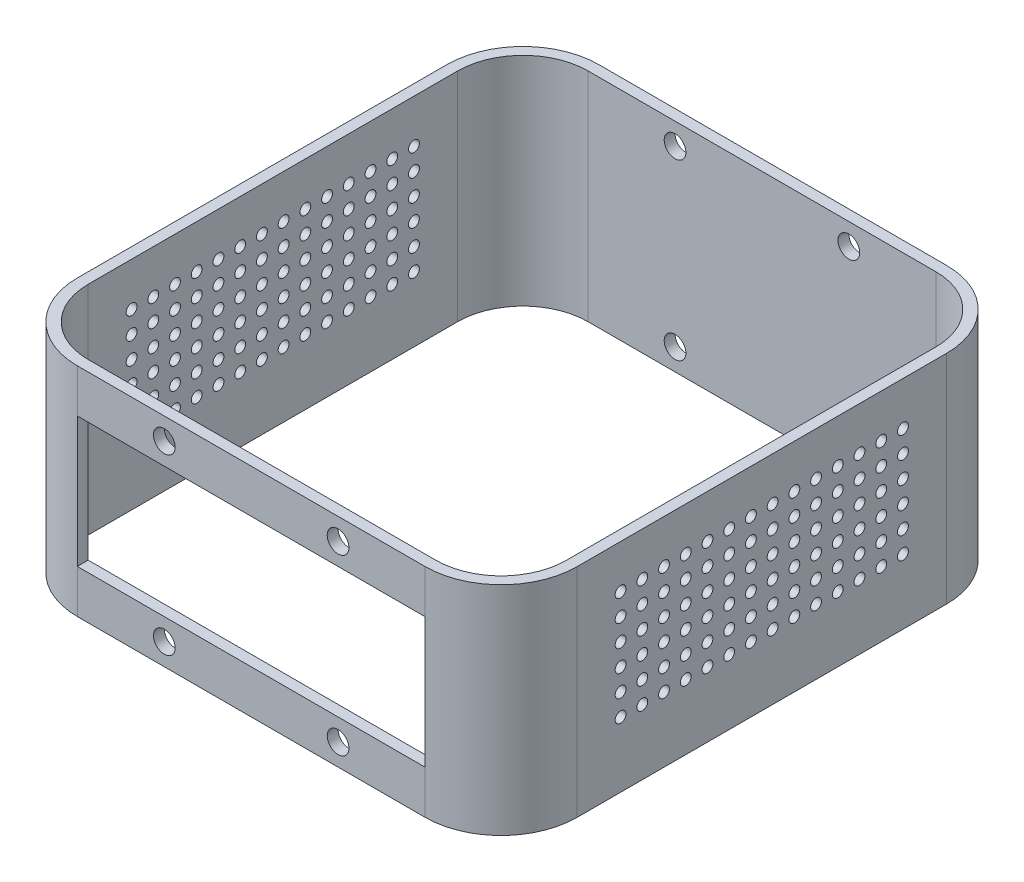
SolidWorks part; units mm, degrees
ref_plane "Front Plane" through (0, 0, 0) normal (0, 0, 1) x (1, 0, 0)
ref_plane "Top Plane" through (0, 0, 0) normal (0, 1, 0) x (1, 0, 0)
ref_plane "Right Plane" through (0, 0, 0) normal (1, 0, 0) x (0, 0, -1)
sketch "Sketch1" plane through (0, 0, 0) normal (0, 1, 0) x (1, 0, 0)
  line L0 (356.5379, 539.6819) -> (1600.9879, 539.6819) construction
  line L1 (-5, 30) -> (-5, 200.15)
  line L2 (30, 0) -> (190.15, 0)
  line L3 (0, 30) -> (0, 200.15)
  line L4 (30, 230.15) -> (190.15, 230.15)
  line L5 (220.15, 30) -> (220.15, 200.15)
  line L6 (30, 235.15) -> (190.15, 235.15)
  line L7 (225.15, 30) -> (225.15, 200.15)
  line L8 (30, -5) -> (190.15, -5)
  arc A0 (30, 230.15) -> (0, 200.15) centre (30, 200.15) ccw
  arc A1 (190.15, 230.15) -> (220.15, 200.15) centre (190.15, 200.15) cw
  arc A2 (220.15, 30) -> (190.15, 0) centre (190.15, 30) cw
  arc A3 (0, 30) -> (30, 0) centre (30, 30) ccw
  arc A4 (30, 235.15) -> (-5, 200.15) centre (30, 200.15) ccw
  arc A5 (190.15, 235.15) -> (225.15, 200.15) centre (190.15, 200.15) cw
  arc A6 (225.15, 30) -> (190.15, -5) centre (190.15, 30) cw
  arc A7 (-5, 30) -> (30, -5) centre (30, 30) ccw
  point P13 (220.15, 0)
  point P16 (0, 0)
  dimension "D3" = 30
  dimension "D1" = 230.15
  dimension "D2" = 220.15
  dimension "D4" = 5
extrude "Boss-Extrude1" add sketch "Sketch1" along normal blind 100
sketch "Sketch3" plane through (-5, 0, 0) normal (-1, 0, 0) x (0, 0, 1)
  line L1 (-200.15, 0) -> (-185.15, 0)
  line L2 (-200.15, 0) -> (-200.15, 20)
  line L3 (-200.15, 20) -> (-185.15, 20)
  line L4 (-185.15, 0) -> (-185.15, 20)
  line L5 (-185.15, 0) -> (-185.15, 20)
  line L6 (-185.15, 0) -> (-170.15, 0)
  line L7 (-170.15, 0) -> (-170.15, 20)
  line L8 (-185.15, 20) -> (-170.15, 20)
  line L9 (-170.15, 0) -> (-170.15, 20)
  line L10 (-170.15, 0) -> (-155.15, 0)
  line L11 (-155.15, 0) -> (-155.15, 20)
  line L12 (-170.15, 20) -> (-155.15, 20)
  line L13 (-155.15, 0) -> (-155.15, 20)
  line L14 (-155.15, 0) -> (-140.15, 0)
  line L15 (-140.15, 0) -> (-140.15, 20)
  line L16 (-155.15, 20) -> (-140.15, 20)
  line L17 (-140.15, 0) -> (-140.15, 20)
  line L18 (-140.15, 0) -> (-125.15, 0)
  line L19 (-125.15, 0) -> (-125.15, 20)
  line L20 (-140.15, 20) -> (-125.15, 20)
  line L21 (-125.15, 0) -> (-125.15, 20)
  line L22 (-125.15, 0) -> (-110.15, 0)
  line L23 (-110.15, 0) -> (-110.15, 20)
  line L24 (-125.15, 20) -> (-110.15, 20)
  line L25 (-110.15, 0) -> (-110.15, 20)
  line L26 (-110.15, 0) -> (-95.15, 0)
  line L27 (-95.15, 0) -> (-95.15, 20)
  line L28 (-110.15, 20) -> (-95.15, 20)
  line L29 (-95.15, 0) -> (-95.15, 20)
  line L30 (-95.15, 0) -> (-80.15, 0)
  line L31 (-80.15, 0) -> (-80.15, 20)
  line L32 (-95.15, 20) -> (-80.15, 20)
  line L33 (-80.15, 0) -> (-80.15, 20)
  line L34 (-80.15, 0) -> (-65.15, 0)
  line L35 (-65.15, 0) -> (-65.15, 20)
  line L36 (-80.15, 20) -> (-65.15, 20)
  line L37 (-65.15, 0) -> (-65.15, 20)
  line L38 (-65.15, 0) -> (-50.15, 0)
  line L39 (-50.15, 0) -> (-50.15, 20)
  line L40 (-65.15, 20) -> (-50.15, 20)
  line L41 (-50.15, 0) -> (-50.15, 20)
  line L42 (-50.15, 0) -> (-35.15, 0)
  line L43 (-35.15, 0) -> (-35.15, 20)
  line L44 (-50.15, 20) -> (-35.15, 20)
  line L45 (-35.15, 0) -> (-35.15, 20)
  line L46 (-35.15, 0) -> (-20.15, 0)
  line L47 (-20.15, 0) -> (-20.15, 20)
  line L48 (-35.15, 20) -> (-20.15, 20)
  line L49 (-20.15, 0) -> (-20.15, 20)
  line L50 (-20.15, 0) -> (-5.15, 0)
  line L51 (-5.15, 0) -> (-5.15, 20)
  line L52 (-20.15, 20) -> (-5.15, 20)
  line L53 (-5.15, 0) -> (-5.15, 20)
  line L54 (-5.15, 0) -> (9.85, 0)
  line L55 (9.85, 0) -> (9.85, 20)
  line L56 (-5.15, 20) -> (9.85, 20)
  line L57 (9.85, 0) -> (9.85, 20)
  line L58 (9.85, 0) -> (24.85, 0)
  line L59 (24.85, 0) -> (24.85, 20)
  line L60 (9.85, 20) -> (24.85, 20)
  line L61 (24.85, 0) -> (24.85, 20)
  line L62 (24.85, 0) -> (39.85, 0)
  line L63 (39.85, 0) -> (39.85, 20)
  line L64 (24.85, 20) -> (39.85, 20)
  line M3 (-200.15, 0) -> (-30, 0)
  line M5 (-30, 100) -> (-200.15, 100)
  line M6 (-200.15, 100) -> (-200.15, 0)
  dimension "D1" = 15
  dimension "D3" = 20
  dimension "D2" = 16
extrude "Boss-Extrude2" [suppressed] add sketch "Sketch3" against normal blind 20 contours L4 M3 M5 M6 | L11 L7 M3 M5 | L19 L15 M3 M5 | L35 L31 M3 M5 | L43 L39 M3 M5 | L51 L47 M3 M5 | L27 L28 L25 L26
sketch "Sketch4" plane through (225.15, 0, 0) normal (1, 0, 0) x (0, 0, -1)
  line L1 (200.15, 0) -> (185.15, 0)
  line L2 (200.15, 0) -> (200.15, 20)
  line L3 (200.15, 20) -> (185.15, 20)
  line L4 (185.15, 0) -> (185.15, 20)
  line L5 (185.15, 0) -> (185.15, 20)
  line L6 (185.15, 0) -> (170.15, 0)
  line L7 (170.15, 0) -> (170.15, 20)
  line L8 (185.15, 20) -> (170.15, 20)
  line L9 (170.15, 0) -> (170.15, 20)
  line L10 (170.15, 0) -> (155.15, 0)
  line L11 (155.15, 0) -> (155.15, 20)
  line L12 (170.15, 20) -> (155.15, 20)
  line L13 (155.15, 0) -> (155.15, 20)
  line L14 (155.15, 0) -> (140.15, 0)
  line L15 (140.15, 0) -> (140.15, 20)
  line L16 (155.15, 20) -> (140.15, 20)
  line L17 (140.15, 0) -> (140.15, 20)
  line L18 (140.15, 0) -> (125.15, 0)
  line L19 (125.15, 0) -> (125.15, 20)
  line L20 (140.15, 20) -> (125.15, 20)
  line L21 (125.15, 0) -> (125.15, 20)
  line L22 (125.15, 0) -> (110.15, 0)
  line L23 (110.15, 0) -> (110.15, 20)
  line L24 (125.15, 20) -> (110.15, 20)
  line L25 (110.15, 0) -> (110.15, 20)
  line L26 (110.15, 0) -> (95.15, 0)
  line L27 (95.15, 0) -> (95.15, 20)
  line L28 (110.15, 20) -> (95.15, 20)
  line L29 (95.15, 0) -> (95.15, 20)
  line L30 (95.15, 0) -> (80.15, 0)
  line L31 (80.15, 0) -> (80.15, 20)
  line L32 (95.15, 20) -> (80.15, 20)
  line L33 (80.15, 0) -> (80.15, 20)
  line L34 (80.15, 0) -> (65.15, 0)
  line L35 (65.15, 0) -> (65.15, 20)
  line L36 (80.15, 20) -> (65.15, 20)
  line L37 (65.15, 0) -> (65.15, 20)
  line L38 (65.15, 0) -> (50.15, 0)
  line L39 (50.15, 0) -> (50.15, 20)
  line L40 (65.15, 20) -> (50.15, 20)
  line L41 (50.15, 0) -> (50.15, 20)
  line L42 (50.15, 0) -> (35.15, 0)
  line L43 (35.15, 0) -> (35.15, 20)
  line L44 (50.15, 20) -> (35.15, 20)
  line L45 (35.15, 0) -> (35.15, 20)
  line L46 (35.15, 0) -> (20.15, 0)
  line L47 (20.15, 0) -> (20.15, 20)
  line L48 (35.15, 20) -> (20.15, 20)
  line L49 (20.15, 0) -> (20.15, 20)
  line L50 (20.15, 0) -> (5.15, 0)
  line L51 (5.15, 0) -> (5.15, 20)
  line L52 (20.15, 20) -> (5.15, 20)
  line L53 (5.15, 0) -> (5.15, 20)
  line L54 (5.15, 0) -> (-9.85, 0)
  line L55 (-9.85, 0) -> (-9.85, 20)
  line L56 (5.15, 20) -> (-9.85, 20)
  line L57 (-9.85, 0) -> (-9.85, 20)
  line L58 (-9.85, 0) -> (-24.85, 0)
  line L59 (-24.85, 0) -> (-24.85, 20)
  line L60 (-9.85, 20) -> (-24.85, 20)
  line L61 (-24.85, 0) -> (-24.85, 20)
  line L62 (-24.85, 0) -> (-39.85, 0)
  line L63 (-39.85, 0) -> (-39.85, 20)
  line L64 (-24.85, 20) -> (-39.85, 20)
  line M5 (30, 0) -> (200.15, 0)
  line M6 (200.15, 0) -> (200.15, 100)
  line M7 (200.15, 100) -> (30, 100)
  dimension "D1" = 15
  dimension "D3" = 20
  dimension "D2" = 16
extrude "Boss-Extrude3" [suppressed] add sketch "Sketch4" against normal blind 20 contours L4 M5 M6 M7 | L11 L7 M5 M7 | L27 L23 M5 M7 | L35 L31 M5 M7 | L43 L39 M5 M7 | L51 L47 M5 M7 | L18 L19 L20 L17
sketch "Sketch12" plane through (0, 0, -235.15) normal (0, 0, -1) x (-1, 0, 0)
  line L0 (-110.075, 100) -> (-110.075, 0) construction
  line L1 (-190.15, 100) -> (-30, 100) construction
  line L2 (-190.15, 0) -> (-30, 0) construction
  line L3 (-190.15, 90) -> (-30, 90) construction
  line L6 (-190.15, 100) -> (-190.15, 0) construction
  line L7 (-30, 100) -> (-30, 0) construction
  line L8 (-190.15, 50) -> (-30, 50) construction
  circle A0 centre (-150.075, 90) radius 5
  circle A1 centre (-70.075, 90) radius 5
  circle A2 centre (-70.075, 10) radius 5
  circle A3 centre (-150.075, 10) radius 5
  dimension "D2" = 10
  dimension "D1" = 10
  dimension "D3" = 40
sketch "Sketch13" plane through (0, 0, 5) normal (0, 0, 1) x (1, 0, 0)
  line L0 (30, 50) -> (190.15, 50) construction
  line L1 (30, 100) -> (30, 0) construction
  line L2 (190.15, 100) -> (190.15, 0) construction
  circle A0 centre (70.075, 90) radius 5
  circle A1 centre (150.075, 90) radius 5
  circle A2 centre (150.075, 10) radius 5
  circle A3 centre (70.075, 10) radius 5
extrude "Cut-Extrude2" cut sketch "Sketch12" against normal blind 10
extrude "Cut-Extrude3" cut sketch "Sketch13" against normal blind 10
sketch "Sketch14" plane through (0, 0, -235.15) normal (0, 0, -1) x (-1, 0, 0)
  line L0 (-110.075, 100) -> (-110.075, 0) construction
  line L1 (-190.15, 100) -> (-30, 100) construction
  line L2 (-190.15, 0) -> (-30, 0) construction
  line L3 (-190.15, 50) -> (-30, 50) construction
  line L4 (-190.15, 100) -> (-190.15, 0) construction
  line L5 (-30, 100) -> (-30, 0) construction
  circle A0 centre (-110.075, 50) radius 42.5
  dimension "D1" = 85
sketch "Sketch16" plane through (0, 0, 5) normal (0, 0, 1) x (1, 0, 0)
  line L0 (30, 80) -> (30, 20)
  line L1 (190.15, 80) -> (190.15, 20)
  line L9 (30, 80) -> (190.15, 80)
  line L10 (30, 80) -> (190.15, 80)
  line L12 (30, 20) -> (190.15, 20)
  line L13 (30, 20) -> (190.15, 20)
  dimension "D1" = 20
  dimension "D2" = 20
extrude "Cut-Extrude4" cut sketch "Sketch16" against normal blind 10
sketch "Sketch17" plane through (225.15, 0, 0) normal (1, 0, 0) x (0, 0, -1)
  line L0 (50, 80) -> (60, 80) construction
  line L8 (50, 20) -> (180.15, 20)
  line L9 (180.15, 20) -> (180.15, 80)
  line L10 (180.15, 80) -> (50, 80)
  line L11 (50, 80) -> (50, 20)
  line L12 (50, 20) -> (180.15, 20) construction
  line L13 (180.15, 20) -> (180.15, 80) construction
  line L14 (180.15, 80) -> (50, 80) construction
  line L15 (50, 80) -> (50, 20) construction
  circle A0 centre (50, 80) radius 2.5
  circle A1 centre (60, 80) radius 2.5
  circle A2 centre (70, 80) radius 2.5
  circle A3 centre (80, 80) radius 2.5
  circle A4 centre (90, 80) radius 2.5
  circle A5 centre (100, 80) radius 2.5
  circle A6 centre (110, 80) radius 2.5
  circle A7 centre (120, 80) radius 2.5
  circle A8 centre (130, 80) radius 2.5
  circle A9 centre (140, 80) radius 2.5
  circle A10 centre (150, 80) radius 2.5
  circle A11 centre (160, 80) radius 2.5
  circle A12 centre (170, 80) radius 2.5
  circle A13 centre (180, 80) radius 2.5
  circle A14 centre (60, 70) radius 2.5
  circle A15 centre (70, 70) radius 2.5
  circle A16 centre (80, 70) radius 2.5
  circle A17 centre (90, 70) radius 2.5
  circle A18 centre (100, 70) radius 2.5
  circle A19 centre (110, 70) radius 2.5
  circle A20 centre (120, 70) radius 2.5
  circle A21 centre (130, 70) radius 2.5
  circle A22 centre (140, 70) radius 2.5
  circle A23 centre (150, 70) radius 2.5
  circle A24 centre (160, 70) radius 2.5
  circle A25 centre (170, 70) radius 2.5
  circle A26 centre (180, 70) radius 2.5
  circle A27 centre (60, 60) radius 2.5
  circle A28 centre (70, 60) radius 2.5
  circle A29 centre (80, 60) radius 2.5
  circle A30 centre (90, 60) radius 2.5
  circle A31 centre (100, 60) radius 2.5
  circle A32 centre (110, 60) radius 2.5
  circle A33 centre (120, 60) radius 2.5
  circle A34 centre (130, 60) radius 2.5
  circle A35 centre (140, 60) radius 2.5
  circle A36 centre (150, 60) radius 2.5
  circle A37 centre (160, 60) radius 2.5
  circle A38 centre (170, 60) radius 2.5
  circle A39 centre (180, 60) radius 2.5
  circle A40 centre (60, 50) radius 2.5
  circle A41 centre (70, 50) radius 2.5
  circle A42 centre (80, 50) radius 2.5
  circle A43 centre (90, 50) radius 2.5
  circle A44 centre (100, 50) radius 2.5
  circle A45 centre (110, 50) radius 2.5
  circle A46 centre (120, 50) radius 2.5
  circle A47 centre (130, 50) radius 2.5
  circle A48 centre (140, 50) radius 2.5
  circle A49 centre (150, 50) radius 2.5
  circle A50 centre (160, 50) radius 2.5
  circle A51 centre (170, 50) radius 2.5
  circle A52 centre (180, 50) radius 2.5
  circle A53 centre (60, 40) radius 2.5
  circle A54 centre (70, 40) radius 2.5
  circle A55 centre (80, 40) radius 2.5
  circle A56 centre (90, 40) radius 2.5
  circle A57 centre (100, 40) radius 2.5
  circle A58 centre (110, 40) radius 2.5
  circle A59 centre (120, 40) radius 2.5
  circle A60 centre (130, 40) radius 2.5
  circle A61 centre (140, 40) radius 2.5
  circle A62 centre (150, 40) radius 2.5
  circle A63 centre (160, 40) radius 2.5
  circle A64 centre (170, 40) radius 2.5
  circle A65 centre (180, 40) radius 2.5
  circle A66 centre (60, 30) radius 2.5
  circle A67 centre (70, 30) radius 2.5
  circle A68 centre (80, 30) radius 2.5
  circle A69 centre (90, 30) radius 2.5
  circle A70 centre (100, 30) radius 2.5
  circle A71 centre (110, 30) radius 2.5
  circle A72 centre (120, 30) radius 2.5
  circle A73 centre (130, 30) radius 2.5
  circle A74 centre (140, 30) radius 2.5
  circle A75 centre (150, 30) radius 2.5
  circle A76 centre (160, 30) radius 2.5
  circle A77 centre (170, 30) radius 2.5
  circle A78 centre (180, 30) radius 2.5
  circle A79 centre (50, 70) radius 2.5
  circle A80 centre (50, 60) radius 2.5
  circle A81 centre (50, 50) radius 2.5
  circle A82 centre (50, 40) radius 2.5
  circle A83 centre (50, 30) radius 2.5
  dimension "D2" = 5
  dimension "D5" = 10
  dimension "D1" = 20
  dimension "D3" = 14
  dimension "D4" = 6
extrude "Cut-Extrude6" cut sketch "Sketch17" against normal through all
